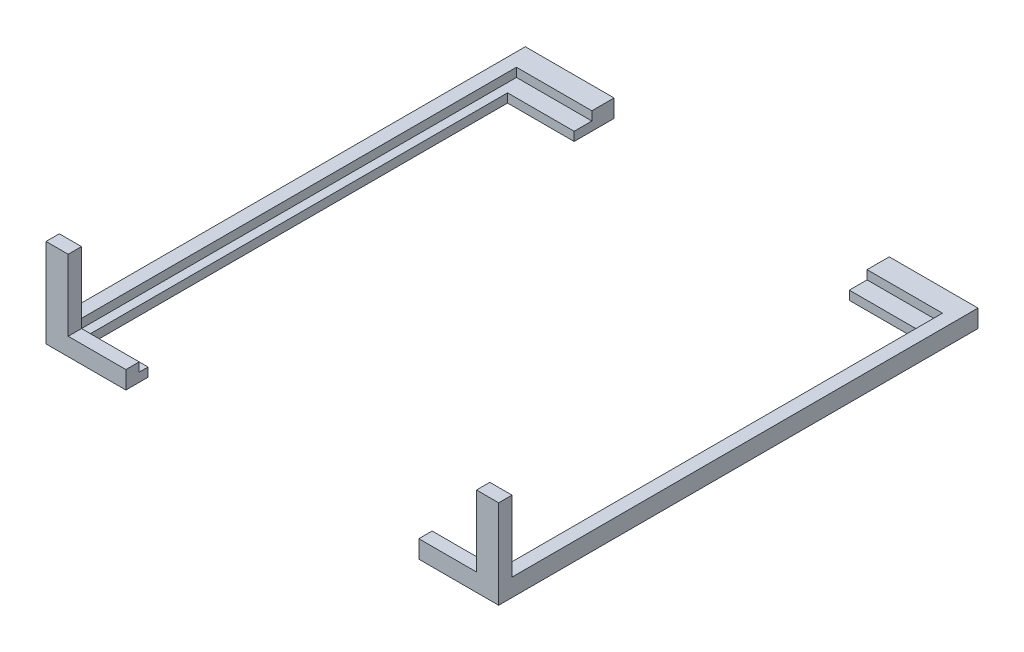
SolidWorks part; units mm, degrees
ref_plane "Front" through (0, 0, 0) normal (0, 0, 1) x (1, 0, 0)
ref_plane "Top" through (0, 0, 0) normal (0, 1, 0) x (1, 0, 0)
ref_plane "Right" through (0, 0, 0) normal (1, 0, 0) x (0, 0, -1)
sketch "草图1" plane through (0, 0, 0) normal (0, 1, 0) x (1, 0, 0)
  line L1 (25.5, -27) -> (-25.5, -27)
  line L2 (25.5, -27) -> (25.5, 27)
  line L3 (25.5, 27) -> (-25.5, 27)
  line L4 (-25.5, -27) -> (-25.5, 27)
  line L5 (25.5, -27) -> (-25.5, 27) construction
  line L6 (25.5, 27) -> (-25.5, -27) construction
  point P0 (0, 0)
  dimension "D1" = 51
  dimension "D2" = 54
extrude "凸台-拉伸1" add sketch "草图1" along normal blind 10
sketch "草图2" plane through (0, 10, 0) normal (0, 1, 0) x (1, 0, 0)
  line L0 (0, 34.677) -> (0, -31.6756) construction
  line L5 (-25.5, -27) -> (25.5, -27) construction
  line L6 (23, -24.5) -> (-23, -24.5)
  line L7 (23, -24.5) -> (23, 22.5)
  line L8 (23, 22.5) -> (-23, 22.5)
  line L9 (-23, -24.5) -> (-23, 22.5)
  line L10 (23, -24.5) -> (-23, 22.5) construction
  line L11 (23, 22.5) -> (-23, -24.5) construction
  point P2 (0, -1)
  dimension "D1" = 46
  dimension "D2" = 47
  dimension "D3" = 2.5
extrude "切除-拉伸1" cut sketch "草图2" against normal through all
sketch "草图3" plane through (0, 10, 0) normal (0, 1, 0) x (1, 0, 0)
  line L0 (0, 45.1498) -> (0, -37.4319) construction
  line L1 (-25.5, -27) -> (25.5, -27) construction
  line L2 (24, -25.5) -> (-24, -25.5)
  line L3 (24, -25.5) -> (24, 24.5)
  line L4 (24, 24.5) -> (-24, 24.5)
  line L5 (-24, -25.5) -> (-24, 24.5)
  line L6 (24, -25.5) -> (-24, 24.5) construction
  line L7 (24, 24.5) -> (-24, -25.5) construction
  point P3 (0, -0.5)
  dimension "D1" = 48
  dimension "D2" = 1.5
  dimension "D3" = 50
extrude "切除-拉伸2" cut sketch "草图3" against normal blind 9
sketch "草图4" plane through (0, 10, 0) normal (0, 1, 0) x (1, 0, 0)
  line L0 (25.5, 27) -> (-25.5, 27) construction
  line L1 (15.5, 22.5) -> (-15.5, 22.5)
  line L2 (15.5, 22.5) -> (15.5, 27)
  line L3 (15.5, 27) -> (-15.5, 27)
  line L4 (-15.5, 22.5) -> (-15.5, 27)
  line L5 (15.5, 22.5) -> (-15.5, 27) construction
  line L6 (15.5, 27) -> (-15.5, 22.5) construction
  line L8 (-25.5, 27) -> (-25.5, -27) construction
  line L9 (25.5, -27) -> (25.5, 27) construction
  line L10 (24, 22.5) -> (-24, 22.5) construction
  point P0 (0, 24.75)
  dimension "D1" = 10
  dimension "D2" = 10
extrude "切除-拉伸3" cut sketch "草图4" against normal through all
sketch "草图5" plane through (0, 10, 0) normal (0, 1, 0) x (1, 0, 0)
  line L0 (0, 37.0353) -> (0, -29.8533) construction
  line L1 (-25.5, 27) -> (-25.5, -27) construction
  line L2 (24, 22.5) -> (-24, 22.5)
  line L3 (24, 22.5) -> (24, 27)
  line L4 (24, 27) -> (-24, 27)
  line L5 (-24, 22.5) -> (-24, 27)
  line L6 (24, 22.5) -> (-24, 27) construction
  line L7 (24, 27) -> (-24, 22.5) construction
  line L8 (-15.5, 27) -> (-25.5, 27) construction
  line L9 (-15.5, 22.5) -> (-24, 22.5) construction
  point P3 (0, 24.75)
  dimension "D1" = 1.5
extrude "切除-拉伸4" cut sketch "草图5" against normal blind 8
sketch "草图6" plane through (0, 10, 0) normal (0, 1, 0) x (1, 0, 0)
  line L0 (0, 49.7907) -> (0, -30.8079) construction
  line L1 (-25.5, 27) -> (-25.5, -27) construction
  line L2 (-25.5, 27) -> (-24, 27)
  line L3 (-25.5, 27) -> (-25.5, -25.5)
  line L4 (-25.5, -25.5) -> (-24, -25.5)
  line L5 (-24, 27) -> (-24, -25.5)
  line L6 (-24, 24.5) -> (-24, -25.5) construction
  line L7 (-24, 27) -> (-25.5, 27) construction
  line L8 (-25.5, -27) -> (25.5, -27) construction
  line L9 (24, 27) -> (24, -25.5)
  line L10 (25.5, -25.5) -> (24, -25.5)
  line L11 (25.5, 27) -> (25.5, -25.5)
  line L12 (25.5, 27) -> (24, 27)
  dimension "D1" = 0
  dimension "D2" = 1.5
extrude "切除-拉伸5" cut sketch "草图6" against normal blind 8
sketch "草图7" plane through (0, 10, 0) normal (0, 1, 0) x (1, 0, 0)
  line L0 (-25.5, -25.5) -> (25.5, -25.5) construction
  line L1 (23, -27) -> (-23, -27)
  line L2 (23, -27) -> (23, -25.5)
  line L3 (23, -25.5) -> (-23, -25.5)
  line L4 (-23, -27) -> (-23, -25.5)
  line L5 (23, -27) -> (-23, -25.5) construction
  line L6 (23, -25.5) -> (-23, -27) construction
  line L7 (-25.5, -27) -> (25.5, -27) construction
  line L8 (-25.5, -25.5) -> (-25.5, -27) construction
  line L9 (25.5, -27) -> (25.5, -25.5) construction
  point P0 (0, -26.25)
  dimension "D1" = 2.5
  dimension "D2" = 2.5
extrude "切除-拉伸6" cut sketch "草图7" against normal blind 8
sketch "草图8" plane through (0, 2, 0) normal (0, 1, 0) x (1, 0, 0)
  line L0 (-23, -27) -> (23, -27) construction
  line L1 (16.5, -29.5) -> (-16.5, -29.5)
  line L2 (16.5, -29.5) -> (16.5, -24.5)
  line L3 (16.5, -24.5) -> (-16.5, -24.5)
  line L4 (-16.5, -29.5) -> (-16.5, -24.5)
  line L5 (16.5, -29.5) -> (-16.5, -24.5) construction
  line L6 (16.5, -24.5) -> (-16.5, -29.5) construction
  line L7 (23, -24.5) -> (-23, -24.5) construction
  line L8 (-25.5, 27) -> (-25.5, -25.5) construction
  point P0 (0, -27)
  dimension "D1" = 9
extrude "切除-拉伸7" cut sketch "草图8" against normal through all
